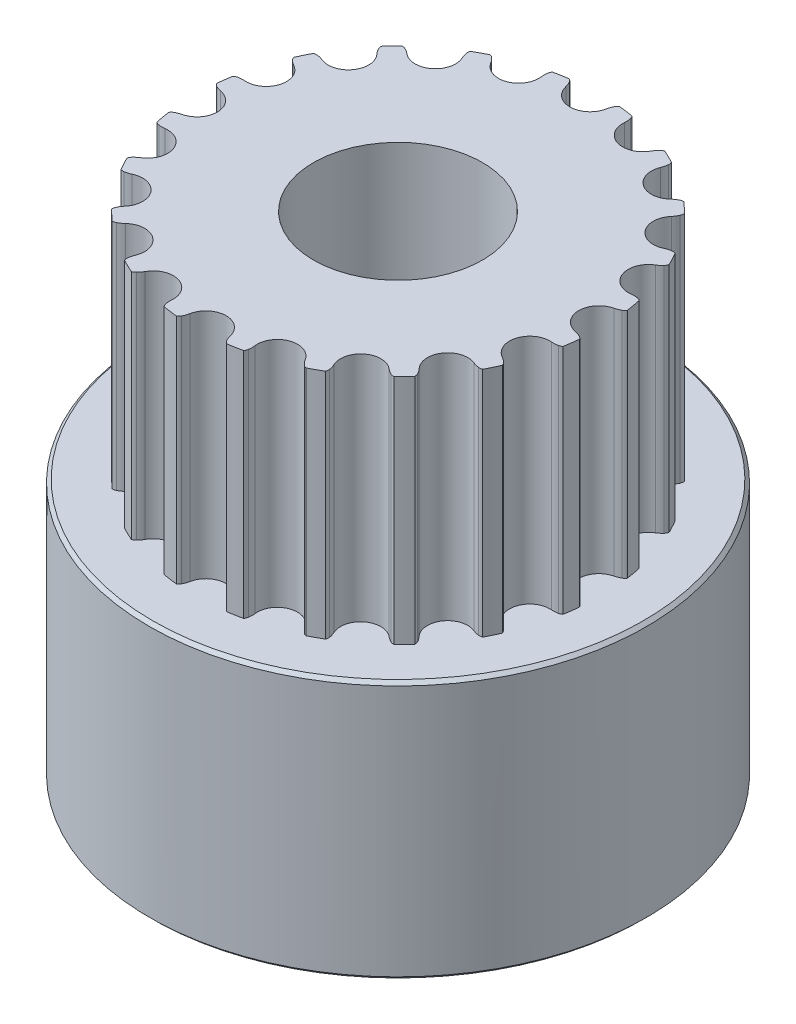
SolidWorks part; units mm, degrees
material "6061 slitina"
ref_plane "Přední rovina" through (0, 0, 0) normal (0, 0, 1) x (1, 0, 0)
ref_plane "Horní rovina" through (0, 0, 0) normal (0, 1, 0) x (1, 0, 0)
ref_plane "Pravá rovina" through (0, 0, 0) normal (1, 0, 0) x (0, 0, -1)
sketch "Skica1" plane through (0, 0, 0) normal (0, 1, 0) x (1, 0, 0)
  circle A0 centre (0, 0) radius 2.5
  arc B0 (-5.7301, 1.0983) -> (-5.3872, 2.2403) centre (-5.6803, 1.7058) ccw
  arc B1 (-5.7301, 1.0983) -> (-5.922, 1.0859) centre (-5.7841, 0.4401) ccw
  arc B2 (-5.922, 1.0859) -> (-6.0197, 1.0387) centre (-5.8743, 0.8624) ccw
  arc B3 (-6.0197, 1.0387) -> (-6.0791, 0.6004) centre (0, 0) ccw
  arc B4 (-6.0791, 0.6004) -> (-5.9974, 0.5289) centre (-5.892, 0.7317) ccw
  arc B5 (-5.9974, 0.5289) -> (-5.8158, 0.466) centre (-5.6927, 1.1148) ccw
  arc B6 (-5.7891, -0.7262) -> (-5.8158, 0.466) centre (-5.9294, -0.133) ccw
  arc B7 (-5.7891, -0.7262) -> (-5.9677, -0.7972) centre (-5.637, -1.3689) ccw
  arc B8 (-5.9677, -0.7972) -> (-6.0461, -0.8723) centre (-5.8532, -0.9951) ccw
  arc B9 (-6.0461, -0.8723) -> (-5.9671, -1.3075) centre (0, 0) ccw
  arc B10 (-5.9671, -1.3075) -> (-5.8673, -1.3503) centre (-5.8297, -1.1248) ccw
  arc B11 (-5.8673, -1.3503) -> (-5.6751, -1.354) centre (-5.7586, -0.6989) ccw
  arc B12 (-5.2813, -2.4796) -> (-5.6751, -1.354) centre (-5.5981, -1.9587) ccw
  arc B13 (-5.2813, -2.4796) -> (-5.4293, -2.6023) centre (-4.9381, -3.0438) ccw
  arc B14 (-5.4293, -2.6023) -> (-5.4806, -2.698) centre (-5.2593, -2.7551) ccw
  arc B15 (-5.4806, -2.698) -> (-5.271, -3.0875) centre (0, 0) ccw
  arc B16 (-5.271, -3.0875) -> (-5.1629, -3.0973) centre (-5.1968, -2.8713) ccw
  arc B17 (-5.1629, -3.0973) -> (-4.979, -3.0415) centre (-5.2608, -2.4442) ccw
  arc B18 (-4.2566, -3.9902) -> (-4.979, -3.0415) centre (-4.7188, -3.5928) ccw
  arc B19 (-4.2566, -3.9902) -> (-4.3594, -4.1527) centre (-3.7559, -4.4208) ccw
  arc B20 (-4.3594, -4.1527) -> (-4.3786, -4.2595) centre (-4.1505, -4.2455) ccw
  arc B21 (-4.3786, -4.2595) -> (-4.059, -4.5652) centre (0, 0) ccw
  arc B22 (-4.059, -4.5652) -> (-3.9531, -4.5412) centre (-4.0552, -4.3366) ccw
  arc B23 (-3.9531, -4.5412) -> (-3.7954, -4.4312) centre (-4.248, -3.9503) ccw
  arc B24 (-2.8152, -5.1103) -> (-3.7954, -4.4312) centre (-3.3776, -4.8751) ccw
  arc B25 (-2.8152, -5.1103) -> (-2.8628, -5.2965) centre (-2.2059, -5.3651) ccw
  arc B26 (-2.8628, -5.2965) -> (-2.8481, -5.4041) centre (-2.6354, -5.3203) ccw
  arc B27 (-2.8481, -5.4041) -> (-2.4496, -5.596) centre (0, 0) ccw
  arc B28 (-2.4496, -5.596) -> (-2.3563, -5.5405) centre (-2.5166, -5.3775) ccw
  arc B29 (-2.3563, -5.5405) -> (-2.2403, -5.3872) centre (-2.8194, -5.0696) ccw
  arc B30 (-1.0983, -5.7301) -> (-2.2403, -5.3872) centre (-1.7058, -5.6803) ccw
  arc B31 (-1.0983, -5.7301) -> (-1.0859, -5.922) centre (-0.4401, -5.7841) ccw
  arc B32 (-1.0859, -5.922) -> (-1.0387, -6.0197) centre (-0.8624, -5.8743) ccw
  arc B33 (-1.0387, -6.0197) -> (-0.6004, -6.0791) centre (0, 0) ccw
  arc B34 (-0.6004, -6.0791) -> (-0.5289, -5.9974) centre (-0.7317, -5.892) ccw
  arc B35 (-0.5289, -5.9974) -> (-0.466, -5.8158) centre (-1.1148, -5.6927) ccw
  arc B36 (0.7262, -5.7891) -> (-0.466, -5.8158) centre (0.133, -5.9294) ccw
  arc B37 (0.7262, -5.7891) -> (0.7972, -5.9677) centre (1.3689, -5.637) ccw
  arc B38 (0.7972, -5.9677) -> (0.8723, -6.0461) centre (0.9951, -5.8532) ccw
  arc B39 (0.8723, -6.0461) -> (1.3075, -5.9671) centre (0, 0) ccw
  arc B40 (1.3075, -5.9671) -> (1.3503, -5.8673) centre (1.1248, -5.8297) ccw
  arc B41 (1.3503, -5.8673) -> (1.354, -5.6751) centre (0.6989, -5.7586) ccw
  arc B42 (2.4796, -5.2813) -> (1.354, -5.6751) centre (1.9587, -5.5981) ccw
  arc B43 (2.4796, -5.2813) -> (2.6023, -5.4293) centre (3.0438, -4.9381) ccw
  arc B44 (2.6023, -5.4293) -> (2.698, -5.4806) centre (2.7551, -5.2593) ccw
  arc B45 (2.698, -5.4806) -> (3.0875, -5.271) centre (0, 0) ccw
  arc B46 (3.0875, -5.271) -> (3.0973, -5.1629) centre (2.8713, -5.1968) ccw
  arc B47 (3.0973, -5.1629) -> (3.0415, -4.979) centre (2.4442, -5.2608) ccw
  arc B48 (3.9902, -4.2566) -> (3.0415, -4.979) centre (3.5928, -4.7188) ccw
  arc B49 (3.9902, -4.2566) -> (4.1527, -4.3594) centre (4.4208, -3.7559) ccw
  arc B50 (4.1527, -4.3594) -> (4.2595, -4.3786) centre (4.2455, -4.1505) ccw
  arc B51 (4.2595, -4.3786) -> (4.5652, -4.059) centre (0, 0) ccw
  arc B52 (4.5652, -4.059) -> (4.5412, -3.9531) centre (4.3366, -4.0552) ccw
  arc B53 (4.5412, -3.9531) -> (4.4312, -3.7954) centre (3.9503, -4.248) ccw
  arc B54 (5.1103, -2.8152) -> (4.4312, -3.7954) centre (4.8751, -3.3776) ccw
  arc B55 (5.1103, -2.8152) -> (5.2965, -2.8628) centre (5.3651, -2.2059) ccw
  arc B56 (5.2965, -2.8628) -> (5.4041, -2.8481) centre (5.3203, -2.6354) ccw
  arc B57 (5.4041, -2.8481) -> (5.596, -2.4496) centre (0, 0) ccw
  arc B58 (5.596, -2.4496) -> (5.5405, -2.3563) centre (5.3775, -2.5166) ccw
  arc B59 (5.5405, -2.3563) -> (5.3872, -2.2403) centre (5.0696, -2.8194) ccw
  arc B60 (5.7301, -1.0983) -> (5.3872, -2.2403) centre (5.6803, -1.7058) ccw
  arc B61 (5.7301, -1.0983) -> (5.922, -1.0859) centre (5.7841, -0.4401) ccw
  arc B62 (5.922, -1.0859) -> (6.0197, -1.0387) centre (5.8743, -0.8624) ccw
  arc B63 (6.0197, -1.0387) -> (6.0791, -0.6004) centre (0, 0) ccw
  arc B64 (6.0791, -0.6004) -> (5.9974, -0.5289) centre (5.892, -0.7317) ccw
  arc B65 (5.9974, -0.5289) -> (5.8158, -0.466) centre (5.6927, -1.1148) ccw
  arc B66 (5.7891, 0.7262) -> (5.8158, -0.466) centre (5.9294, 0.133) ccw
  arc B67 (5.7891, 0.7262) -> (5.9677, 0.7972) centre (5.637, 1.3689) ccw
  arc B68 (5.9677, 0.7972) -> (6.0461, 0.8723) centre (5.8532, 0.9951) ccw
  arc B69 (6.0461, 0.8723) -> (5.9671, 1.3075) centre (0, 0) ccw
  arc B70 (5.9671, 1.3075) -> (5.8673, 1.3503) centre (5.8297, 1.1248) ccw
  arc B71 (5.8673, 1.3503) -> (5.6751, 1.354) centre (5.7586, 0.6989) ccw
  arc B72 (5.2813, 2.4796) -> (5.6751, 1.354) centre (5.5981, 1.9587) ccw
  arc B73 (5.2813, 2.4796) -> (5.4293, 2.6023) centre (4.9381, 3.0438) ccw
  arc B74 (5.4293, 2.6023) -> (5.4806, 2.698) centre (5.2593, 2.7551) ccw
  arc B75 (5.4806, 2.698) -> (5.271, 3.0875) centre (0, 0) ccw
  arc B76 (5.271, 3.0875) -> (5.1629, 3.0973) centre (5.1968, 2.8713) ccw
  arc B77 (5.1629, 3.0973) -> (4.979, 3.0415) centre (5.2608, 2.4442) ccw
  arc B78 (4.2566, 3.9902) -> (4.979, 3.0415) centre (4.7188, 3.5928) ccw
  arc B79 (4.2566, 3.9902) -> (4.3594, 4.1527) centre (3.7559, 4.4208) ccw
  arc B80 (4.3594, 4.1527) -> (4.3786, 4.2595) centre (4.1505, 4.2455) ccw
  arc B81 (4.3786, 4.2595) -> (4.059, 4.5652) centre (0, 0) ccw
  arc B82 (4.059, 4.5652) -> (3.9531, 4.5412) centre (4.0552, 4.3366) ccw
  arc B83 (3.9531, 4.5412) -> (3.7954, 4.4312) centre (4.248, 3.9503) ccw
  arc B84 (2.8152, 5.1103) -> (3.7954, 4.4312) centre (3.3776, 4.8751) ccw
  arc B85 (2.8152, 5.1103) -> (2.8628, 5.2965) centre (2.2059, 5.3651) ccw
  arc B86 (2.8628, 5.2965) -> (2.8481, 5.4041) centre (2.6354, 5.3203) ccw
  arc B87 (2.8481, 5.4041) -> (2.4496, 5.596) centre (0, 0) ccw
  arc B88 (2.4496, 5.596) -> (2.3563, 5.5405) centre (2.5166, 5.3775) ccw
  arc B89 (2.3563, 5.5405) -> (2.2403, 5.3872) centre (2.8194, 5.0696) ccw
  arc B90 (1.0983, 5.7301) -> (2.2403, 5.3872) centre (1.7058, 5.6803) ccw
  arc B91 (1.0983, 5.7301) -> (1.0859, 5.922) centre (0.4401, 5.7841) ccw
  arc B92 (1.0859, 5.922) -> (1.0387, 6.0197) centre (0.8624, 5.8743) ccw
  arc B93 (1.0387, 6.0197) -> (0.6004, 6.0791) centre (0, 0) ccw
  arc B94 (0.6004, 6.0791) -> (0.5289, 5.9974) centre (0.7317, 5.892) ccw
  arc B95 (0.5289, 5.9974) -> (0.466, 5.8158) centre (1.1148, 5.6927) ccw
  arc B96 (-0.7262, 5.7891) -> (0.466, 5.8158) centre (-0.133, 5.9294) ccw
  arc B97 (-0.7262, 5.7891) -> (-0.7972, 5.9677) centre (-1.3689, 5.637) ccw
  arc B98 (-0.7972, 5.9677) -> (-0.8723, 6.0461) centre (-0.9951, 5.8532) ccw
  arc B99 (-0.8723, 6.0461) -> (-1.3075, 5.9671) centre (0, 0) ccw
  arc B100 (-1.3075, 5.9671) -> (-1.3503, 5.8673) centre (-1.1248, 5.8297) ccw
  arc B101 (-1.3503, 5.8673) -> (-1.354, 5.6751) centre (-0.6989, 5.7586) ccw
  arc B102 (-2.4796, 5.2813) -> (-1.354, 5.6751) centre (-1.9587, 5.5981) ccw
  arc B103 (-2.4796, 5.2813) -> (-2.6023, 5.4293) centre (-3.0438, 4.9381) ccw
  arc B104 (-2.6023, 5.4293) -> (-2.698, 5.4806) centre (-2.7551, 5.2593) ccw
  arc B105 (-2.698, 5.4806) -> (-3.0875, 5.271) centre (0, 0) ccw
  arc B106 (-3.0875, 5.271) -> (-3.0973, 5.1629) centre (-2.8713, 5.1968) ccw
  arc B107 (-3.0973, 5.1629) -> (-3.0415, 4.979) centre (-2.4442, 5.2608) ccw
  arc B108 (-3.9902, 4.2566) -> (-3.0415, 4.979) centre (-3.5928, 4.7188) ccw
  arc B109 (-3.9902, 4.2566) -> (-4.1527, 4.3594) centre (-4.4208, 3.7559) ccw
  arc B110 (-4.1527, 4.3594) -> (-4.2595, 4.3786) centre (-4.2455, 4.1505) ccw
  arc B111 (-4.2595, 4.3786) -> (-4.5652, 4.059) centre (0, 0) ccw
  arc B112 (-4.5652, 4.059) -> (-4.5412, 3.9531) centre (-4.3366, 4.0552) ccw
  arc B113 (-4.5412, 3.9531) -> (-4.4312, 3.7954) centre (-3.9503, 4.248) ccw
  arc B114 (-5.1103, 2.8152) -> (-4.4312, 3.7954) centre (-4.8751, 3.3776) ccw
  arc B115 (-5.1103, 2.8152) -> (-5.2965, 2.8628) centre (-5.3651, 2.2059) ccw
  arc B116 (-5.2965, 2.8628) -> (-5.4041, 2.8481) centre (-5.3203, 2.6354) ccw
  arc B117 (-5.4041, 2.8481) -> (-5.596, 2.4496) centre (0, 0) ccw
  arc B118 (-5.596, 2.4496) -> (-5.5405, 2.3563) centre (-5.3775, 2.5166) ccw
  arc B119 (-5.5405, 2.3563) -> (-5.3872, 2.2403) centre (-5.0696, 2.8194) ccw
  dimension "D1" = 5
sketch_block_instance "Blok1-1"
sketch_block "Blok1"
extrude "Přidat vysunutím1" add sketch "Skica1" along normal blind 7 from offset 7.8
sketch "Skica2" plane through (0, 7.8, 0) normal (0, -1, 0) x (1, 0, 0)
  circle A0 centre (0, 0) radius 3.5
  circle A1 centre (0, 0) radius 2.5 construction
  circle A2 centre (0, 0) radius 2.5
  dimension "D1" = 7
extrude "Přidat vysunutím2" add sketch "Skica2" along normal blind 7.8
sketch "Skica3" plane through (0, 14.8, 0) normal (0, 1, 0) x (1, 0, 0)
  circle A0 centre (0, 0) radius 3.5
  circle A1 centre (0, 0) radius 2.5 construction
  circle A2 centre (0, 0) radius 2.5
  dimension "D1" = 7
sketch "Skica5" plane through (0, 16, 0) normal (0, 1, 0) x (1, 0, 0)
  circle A0 centre (0, 0) radius 7.5
  circle A3 centre (0, 0) radius 3.5 construction
  circle A4 centre (0, 0) radius 3.5
  dimension "D1" = 15
sketch "Skica6" plane through (0, 0, 0) normal (0, -1, 0) x (1, 0, 0)
  circle A0 centre (0, 0) radius 7.5
  circle A1 centre (0, 0) radius 3.5 construction
  circle A2 centre (0, 0) radius 3.5
  circle A3 centre (0, 0) radius 7.5 construction
extrude "Přidat vysunutím5" add sketch "Skica6" against normal up to surface (7.8 mm away) separate body up to face at (0, 7.8, 0)
chamfer "Zkosení3" distance 0.1 angle 45 2 edges at (0, 0, -7.5) (0, 7.8, 7.5)
sketch "Sketch7" plane through (0, 0, 0) normal (0, -1, 0) x (1, 0, 0)
  circle A1 centre (0, 0) radius 4.05
  dimension "D1" = 8.1
sketch "Sketch8" plane through (0, 16, 0) normal (0, 1, 0) x (1, 0, 0)
  circle A0 centre (0, 0) radius 6.65
ref_plane "Plane1" through (0, 0, -7.5) normal (0, 0, -1) x (-1, 0, 0)
ref_plane "Plane2" through (-7.5, 0, 0) normal (-1, 0, 0) x (0, 0, 1)
sketch "Sketch19" plane through (0, 0, -7.5) normal (0, 0, -1) x (-1, 0, 0)
  line L0 (0, 0.1) -> (0, 7.7)
  line L1 (7.5, 0.1) -> (-7.5, 0.1) construction
  line L2 (7.5, 7.7) -> (-7.5, 7.7) construction
  circle A0 centre (0, 3.9) radius 1.5
extrude "Cut-Extrude6" cut sketch "Sketch19" against normal blind 8 contours A0
sketch "Sketch20" plane through (-7.5, 0, 0) normal (-1, 0, 0) x (0, 0, 1)
  line L0 (0, 0.1) -> (0, 7.7)
  line L1 (-7.5, 0.1) -> (7.5, 0.1) construction
  line L2 (7.5, 7.7) -> (-7.5, 7.7) construction
  circle A0 centre (0, 3.9) radius 1.5
extrude "Cut-Extrude7" cut sketch "Sketch20" against normal blind 8 contours A0
sketch "Sketch21" plane through (0, 16, 0) normal (0, 1, 0) x (1, 0, 0)
  circle A0 centre (0, 0) radius 2.55
extrude "Cut-Extrude8" cut sketch "Sketch21" against normal blind 30
